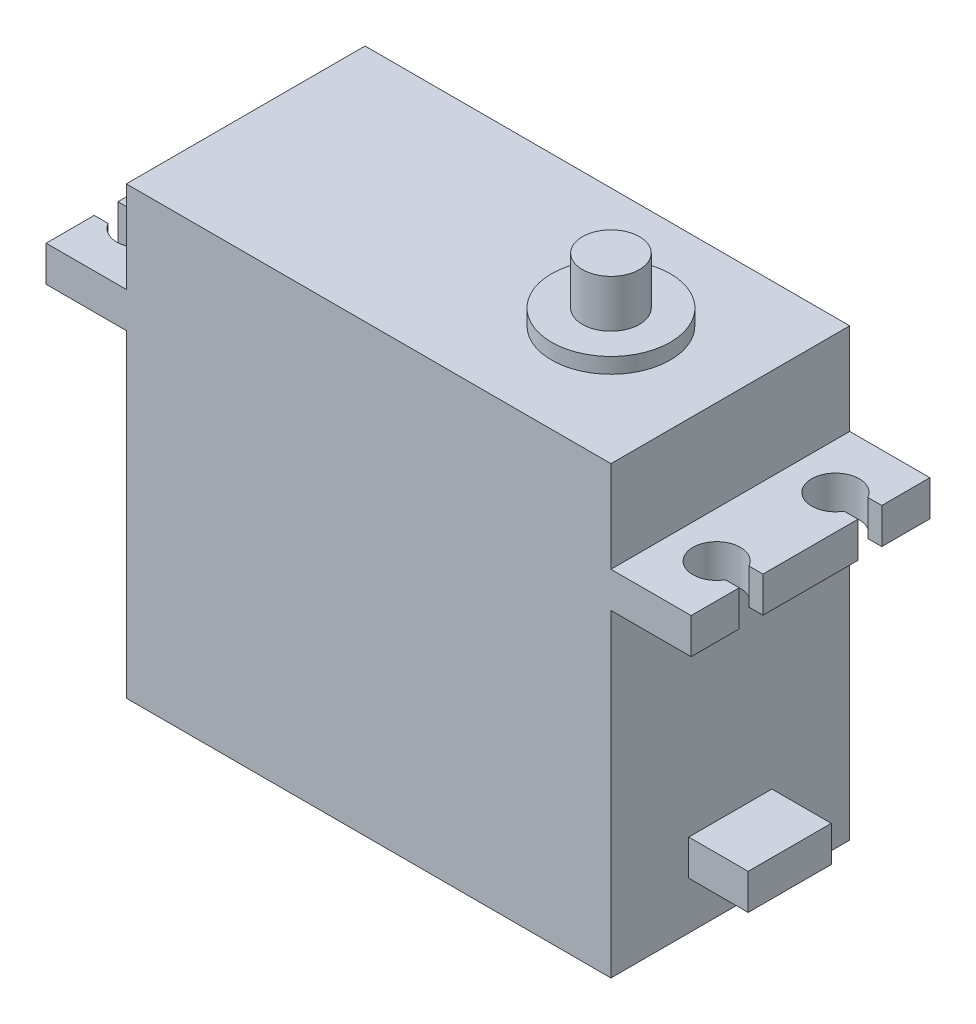
SolidWorks part; units mm, degrees
ref_plane "Front Plane" through (0, 0, 0) normal (0, 0, 1) x (1, 0, 0)
ref_plane "Top Plane" through (0, 0, 0) normal (0, 1, 0) x (1, 0, 0)
ref_plane "Right Plane" through (0, 0, 0) normal (1, 0, 0) x (0, 0, -1)
sketch "Sketch2" plane through (0, 0, 0) normal (0, 1, 0) x (1, 0, 0)
  line L0 (0, 0) -> (0, 10.05) construction
  line L1 (0, 0) -> (10.05, 0) construction
  line L2 (0, 0) -> (0, -10.05) construction
  line L3 (0, 0) -> (-30.75, 0) construction
  line L4 (-34.6, 5) -> (-34.6, -5) construction
  line L5 (-30.75, 10.05) -> (10.05, 10.05)
  line L6 (-30.75, 10.05) -> (-30.75, -10.05)
  line L7 (-30.75, -10.05) -> (10.05, -10.05)
  line L8 (10.05, 10.05) -> (10.05, -10.05)
  line L9 (-30.75, 10.05) -> (-37.5, 10.05) construction
  line L10 (-37.5, 10.05) -> (-37.5, -10.05) construction
  line L11 (-37.5, -10.05) -> (-30.75, -10.05) construction
  line L12 (-10.35, 10.05) -> (-10.35, -10.05) construction
  line L13 (13.9, 5) -> (13.9, -5) construction
  line L14 (-36.6, 5) -> (-37.5, 5) construction
  line L15 (10.05, 10.05) -> (16.8, 10.05) construction
  line L16 (16.8, 10.05) -> (16.8, -10.05) construction
  line L17 (16.8, -10.05) -> (10.05, -10.05) construction
  line L18 (10.05, 3.5) -> (15.05, 3.5) construction
  line L19 (15.05, 3.5) -> (15.05, -3.5) construction
  line L20 (15.05, -3.5) -> (10.05, -3.5) construction
  circle A0 centre (0, 0) radius 2.4
  circle A1 centre (0, 0) radius 10.05 construction
  circle A2 centre (-34.6, 5) radius 2
  circle A3 centre (-34.6, -5) radius 2
  circle A4 centre (13.9, -5) radius 2
  circle A5 centre (13.9, 5) radius 2
  circle A6 centre (0, 0) radius 5 construction
  dimension "D1" = 4.8
  dimension "D6" = 4
  dimension "D8" = 10
  dimension "D2" = 40.8
  dimension "D3" = 20.1
  dimension "D4" = 10
  dimension "D5" = 48.5
  dimension "D7" = 0.9
  dimension "D9" = 54.3
  dimension "D10" = 7
  dimension "D11" = 5
sketch "Sketch3" plane through (0, 0, 0) normal (0, 0, 1) x (1, 0, 0)
  line L0 (-30.75, 0) -> (-30.75, 26.8)
  line L1 (-30.75, 26.8) -> (-37.5, 26.8)
  line L2 (-37.5, 26.8) -> (-37.5, 29.8)
  line L3 (-37.5, 29.8) -> (-30.75, 29.8)
  line L4 (-30.75, 29.8) -> (-30.75, 37.5)
  line L5 (-30.75, 37.5) -> (10.05, 37.5)
  line L6 (10.05, 37.5) -> (10.05, 29.8)
  line L7 (10.05, 29.8) -> (16.8, 29.8)
  line L8 (16.8, 29.8) -> (16.8, 26.8)
  line L9 (16.8, 26.8) -> (10.05, 26.8)
  line L10 (10.05, 26.8) -> (10.05, 0)
  line L11 (10.05, 0) -> (-30.75, 0)
  line L12 (-10.35, 0) -> (-10.35, 37.5) construction
  line L13 (2.4, 0) -> (2.4, 42.8) construction
  line L14 (2.4, 0) -> (-2.4, 0) construction
  line L15 (2.4, 42.8) -> (-2.4, 42.8) construction
  line L16 (-2.4, 42.8) -> (-2.4, 0) construction
  line L17 (10.05, 0) -> (-10.05, 0) construction
  line L18 (-5, 38.8) -> (5, 38.8) construction
  line L19 (-5, 0) -> (-5, 38.8) construction
  line L20 (5, 38.8) -> (5, 0) construction
  line L21 (10.05, 4) -> (15.05, 4) construction
  line L22 (15.05, 4) -> (15.05, 7) construction
  line L23 (15.05, 7) -> (10.05, 7) construction
  line L24 (5, 38.8) -> (19.8, 38.8) construction
  line L26 (19.8, 38.8) -> (19.8, 26.8) construction
  line L28 (16.8, 26.8) -> (19.8, 26.8) construction
  dimension "D1" = 26.8
  dimension "D2" = 3
  dimension "D3" = 4
  dimension "D4" = 38.8
  dimension "D5" = 1.3
  dimension "D6" = 12
  dimension "D7" = 7
  dimension "D8" = 4
  dimension "D9" = 37.5
extrude "Boss-Extrude1" add sketch "Sketch3" along normal up to vertex (10.05 mm away) from vertex at -10.05 starting at point (-30.75, 0, -10.05)
sketch "Sketch4" plane through (0, 29.8, 0) normal (0, 1, 0) x (1, 0, 0)
  line L0 (-10.35, 10.05) -> (-10.35, -10.05) construction
  line L1 (-10.35, 10.05) -> (-10.35, -10.05) construction
  line L2 (-37.5, 10.05) -> (-37.5, -10.05) construction
  line L4 (-37.5, 6) -> (-37.5, 4)
  line L5 (16.8, -6) -> (15.6321, -6)
  line L6 (-10.35, 0) -> (-37.5, 0) construction
  line L7 (-37.5, 4) -> (-36.3321, 4)
  line L8 (-37.5, 6) -> (-36.3321, 6)
  line L9 (-34.6, 5) -> (-37.5, 5) construction
  line L10 (-37.5, -4) -> (-37.5, -6)
  line L11 (-37.5, -4) -> (-36.3321, -4)
  line L12 (-37.5, -6) -> (-36.3321, -6)
  line L13 (16.8, -4) -> (16.8, -6)
  line L14 (16.8, -4) -> (15.6321, -4)
  line L15 (16.8, 4) -> (15.6321, 4)
  line L16 (16.8, 6) -> (16.8, 4)
  line L17 (16.8, 6) -> (15.6321, 6)
  circle A0 centre (-34.6, -5) radius 2 construction
  circle A1 centre (-34.6, 5) radius 2 construction
  circle A2 centre (13.9, 5) radius 2 construction
  circle A3 centre (13.9, -5) radius 2 construction
  arc A4 (-36.3321, -6) -> (-36.3321, -4) centre (-34.6, -5) ccw
  arc A5 (-36.3321, 4) -> (-36.3321, 6) centre (-34.6, 5) ccw
  arc A6 (15.6321, 6) -> (15.6321, 4) centre (13.9, 5) ccw
  arc A7 (15.6321, -4) -> (15.6321, -6) centre (13.9, -5) ccw
  dimension "D1" = 2
extrude "Cut-Extrude1" cut sketch "Sketch4" against normal through all
sketch "Sketch5" plane through (0, 37.5, 0) normal (0, 1, 0) x (1, 0, 0)
  circle A0 centre (0, 0) radius 5 construction
  circle A1 centre (0, 0) radius 5
extrude "Boss-Extrude2" add sketch "Sketch5" along normal up to vertex (1.3 mm away) up to point (-5, 38.8, 0)
sketch "Sketch6" plane through (0, 38.8, 0) normal (0, 1, 0) x (1, 0, 0)
  circle A0 centre (0, 0) radius 2.4 construction
  circle A1 centre (0, 0) radius 2.4
extrude "Boss-Extrude3" add sketch "Sketch6" along normal up to vertex (4 mm away) up to point (-2.4, 42.8, 0)
sketch "Sketch7" plane through (0, 38.8, 0) normal (0, 1, 0) x (1, 0, 0)
  circle A0 centre (0, 0) radius 2.85
  dimension "D1" = 5.7
sketch "Sketch8" plane through (10.05, 0, 0) normal (1, 0, 0) x (0, 0, -1)
  line L1 (-3.5, 7) -> (3.5, 7)
  line L2 (-3.5, 7) -> (-3.5, 4)
  line L3 (-3.5, 4) -> (3.5, 4)
  line L4 (3.5, 7) -> (3.5, 4)
extrude "Boss-Extrude4" add sketch "Sketch8" along normal up to vertex (5 mm away) up to point (15.05, 7, 0)
